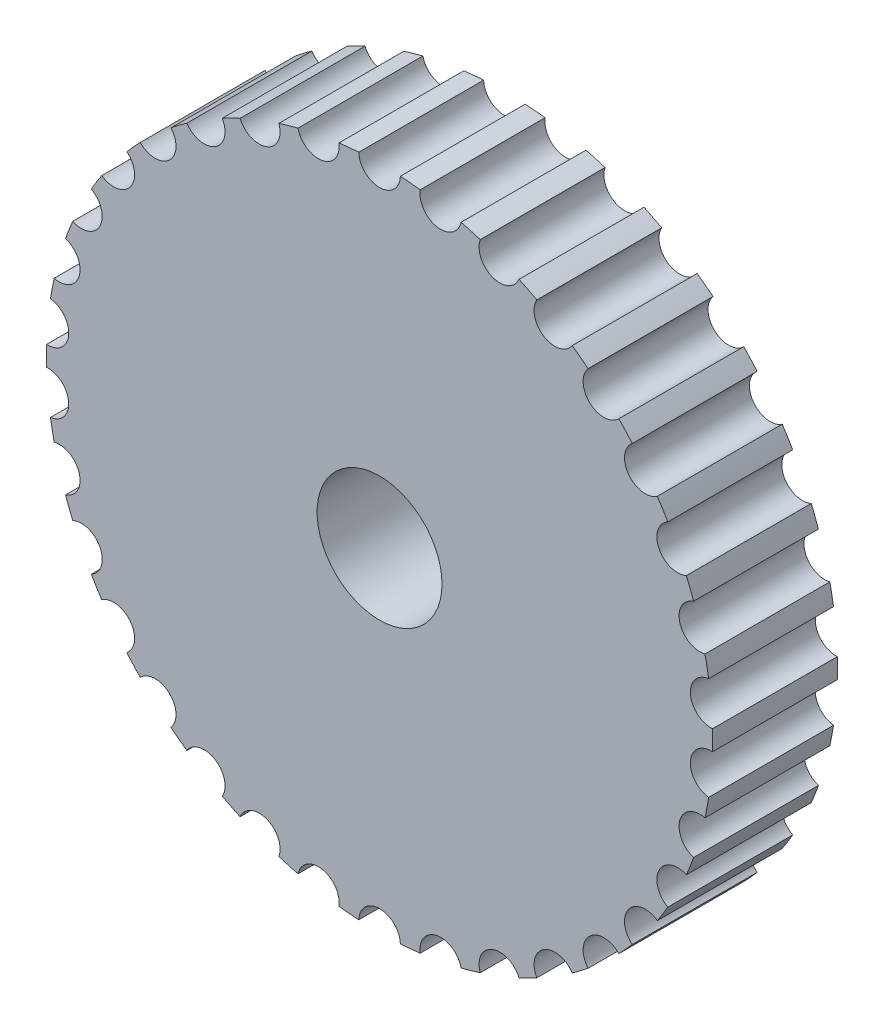
SolidWorks part; units mm, degrees
ref_plane "前视基准面" through (0, 0, 0) normal (0, 0, 1) x (1, 0, 0)
ref_plane "上视基准面" through (0, 0, 0) normal (0, 1, 0) x (1, 0, 0)
ref_plane "右视基准面" through (0, 0, 0) normal (1, 0, 0) x (0, 0, -1)
other "Configuration Table"
sketch "Sketch1" plane through (0, 0, 0) normal (0, 0, 1) x (1, 0, 0)
  circle A0 centre (0, 0) radius 1.5
  arc A1 (-0.4998, 7.9844) -> (-0.9759, 7.9403) centre (0, 0) ccw
  arc A2 (-0.4998, 7.9844) -> (0.4998, 7.9844) centre (0, 8) ccw
  arc A3 (0.9759, 7.9403) -> (1.9584, 7.7566) centre (1.47, 7.8638) ccw
  arc A4 (2.4183, 7.6257) -> (3.3503, 7.2647) centre (2.8899, 7.4598) ccw
  arc A5 (3.7783, 7.0515) -> (4.6281, 6.5254) centre (4.2115, 6.8017) ccw
  arc A6 (5.0097, 6.2372) -> (5.7484, 5.5638) centre (5.3896, 5.9121) ccw
  arc A7 (6.0705, 5.2105) -> (6.6728, 4.4128) centre (6.3841, 4.8211) ccw
  arc A8 (6.9246, 4.0063) -> (7.3701, 3.1116) centre (7.1613, 3.5659) ccw
  arc A9 (7.5428, 2.6657) -> (7.8163, 1.7043) centre (7.6946, 2.1893) ccw
  arc A10 (7.9042, 1.2343) -> (7.9964, 0.2391) centre (7.9659, 0.7381) ccw
  arc A11 (7.9964, -0.2391) -> (7.9042, -1.2343) centre (7.9659, -0.7381) ccw
  arc A12 (7.8163, -1.7043) -> (7.5428, -2.6657) centre (7.6946, -2.1893) ccw
  arc A13 (7.3701, -3.1116) -> (6.9246, -4.0063) centre (7.1613, -3.5659) ccw
  arc A14 (6.6728, -4.4128) -> (6.0705, -5.2105) centre (6.3841, -4.8211) ccw
  arc A15 (5.7484, -5.5638) -> (5.0097, -6.2372) centre (5.3896, -5.9121) ccw
  arc A16 (4.6281, -6.5254) -> (3.7783, -7.0515) centre (4.2115, -6.8017) ccw
  arc A17 (3.3503, -7.2647) -> (2.4183, -7.6257) centre (2.8899, -7.4598) ccw
  arc A18 (1.9584, -7.7566) -> (0.9759, -7.9403) centre (1.47, -7.8638) ccw
  arc A19 (0.4998, -7.9844) -> (-0.4998, -7.9844) centre (0, -8) ccw
  arc A20 (-0.9759, -7.9403) -> (-1.9584, -7.7566) centre (-1.47, -7.8638) ccw
  arc A21 (-2.4183, -7.6257) -> (-3.3503, -7.2647) centre (-2.8899, -7.4598) ccw
  arc A22 (-3.7783, -7.0515) -> (-4.6281, -6.5254) centre (-4.2115, -6.8017) ccw
  arc A23 (-5.0097, -6.2372) -> (-5.7484, -5.5638) centre (-5.3896, -5.9121) ccw
  arc A24 (-6.0705, -5.2105) -> (-6.6728, -4.4128) centre (-6.3841, -4.8211) ccw
  arc A25 (-6.9246, -4.0063) -> (-7.3701, -3.1116) centre (-7.1613, -3.5659) ccw
  arc A26 (-7.5428, -2.6657) -> (-7.8163, -1.7043) centre (-7.6946, -2.1893) ccw
  arc A27 (-7.9042, -1.2343) -> (-7.9964, -0.2391) centre (-7.9659, -0.7381) ccw
  arc A28 (-7.9964, 0.2391) -> (-7.9042, 1.2343) centre (-7.9659, 0.7381) ccw
  arc A29 (-7.8163, 1.7043) -> (-7.5428, 2.6657) centre (-7.6946, 2.1893) ccw
  arc A30 (-7.3701, 3.1116) -> (-6.9246, 4.0063) centre (-7.1613, 3.5659) ccw
  arc A31 (-6.6728, 4.4128) -> (-6.0705, 5.2105) centre (-6.3841, 4.8211) ccw
  arc A32 (-5.7484, 5.5638) -> (-5.0097, 6.2372) centre (-5.3896, 5.9121) ccw
  arc A33 (-4.6281, 6.5254) -> (-3.7783, 7.0515) centre (-4.2115, 6.8017) ccw
  arc A34 (-3.3503, 7.2647) -> (-2.4183, 7.6257) centre (-2.8899, 7.4598) ccw
  arc A35 (-1.9584, 7.7566) -> (-0.9759, 7.9403) centre (-1.47, 7.8638) ccw
  arc A36 (-3.3503, 7.2647) -> (-3.7783, 7.0515) centre (0, 0) ccw
  arc A37 (-1.9584, 7.7566) -> (-2.4183, 7.6257) centre (0, 0) ccw
  arc A38 (-4.6281, 6.5254) -> (-5.0097, 6.2372) centre (0, 0) ccw
  arc A39 (-5.7484, 5.5638) -> (-6.0705, 5.2105) centre (0, 0) ccw
  arc A40 (-6.6728, 4.4128) -> (-6.9246, 4.0063) centre (0, 0) ccw
  arc A41 (-7.3701, 3.1116) -> (-7.5428, 2.6657) centre (0, 0) ccw
  arc A42 (-7.8163, 1.7043) -> (-7.9042, 1.2343) centre (0, 0) ccw
  arc A43 (-7.9964, 0.2391) -> (-7.9964, -0.2391) centre (0, 0) ccw
  arc A44 (-7.9042, -1.2343) -> (-7.8163, -1.7043) centre (0, 0) ccw
  arc A45 (-7.5428, -2.6657) -> (-7.3701, -3.1116) centre (0, 0) ccw
  arc A46 (-5.0097, -6.2372) -> (-4.6281, -6.5254) centre (0, 0) ccw
  arc A47 (-6.9246, -4.0063) -> (-6.6728, -4.4128) centre (0, 0) ccw
  arc A48 (-6.0705, -5.2105) -> (-5.7484, -5.5638) centre (0, 0) ccw
  arc A49 (-3.7783, -7.0515) -> (-3.3503, -7.2647) centre (0, 0) ccw
  arc A50 (-2.4183, -7.6257) -> (-1.9584, -7.7566) centre (0, 0) ccw
  arc A51 (-0.9759, -7.9403) -> (-0.4998, -7.9844) centre (0, 0) ccw
  arc A52 (0.4998, -7.9844) -> (0.9759, -7.9403) centre (0, 0) ccw
  arc A53 (1.9584, -7.7566) -> (2.4183, -7.6257) centre (0, 0) ccw
  arc A54 (3.3503, -7.2647) -> (3.7783, -7.0515) centre (0, 0) ccw
  arc A55 (4.6281, -6.5254) -> (5.0097, -6.2372) centre (0, 0) ccw
  arc A56 (5.7484, -5.5638) -> (6.0705, -5.2105) centre (0, 0) ccw
  arc A57 (6.6728, -4.4128) -> (6.9246, -4.0063) centre (0, 0) ccw
  arc A58 (0.9759, 7.9403) -> (0.4998, 7.9844) centre (0, 0) ccw
  arc A59 (2.4183, 7.6257) -> (1.9584, 7.7566) centre (0, 0) ccw
  arc A60 (3.7783, 7.0515) -> (3.3503, 7.2647) centre (0, 0) ccw
  arc A61 (5.0097, 6.2372) -> (4.6281, 6.5254) centre (0, 0) ccw
  arc A62 (6.0705, 5.2105) -> (5.7484, 5.5638) centre (0, 0) ccw
  arc A63 (6.9246, 4.0063) -> (6.6728, 4.4128) centre (0, 0) ccw
  arc A64 (7.5428, 2.6657) -> (7.3701, 3.1116) centre (0, 0) ccw
  arc A65 (7.9042, 1.2343) -> (7.8163, 1.7043) centre (0, 0) ccw
  arc A66 (7.9964, -0.2391) -> (7.9964, 0.2391) centre (0, 0) ccw
  arc A67 (7.8163, -1.7043) -> (7.9042, -1.2343) centre (0, 0) ccw
  arc A68 (7.3701, -3.1116) -> (7.5428, -2.6657) centre (0, 0) ccw
  point P108 (0, 0)
  dimension "D1" = 3
  dimension "D2" = 16
  dimension "D3" = 1
  dimension "D4" = 34
extrude "Boss-Extrude1" add sketch "Sketch1" along normal blind 3
